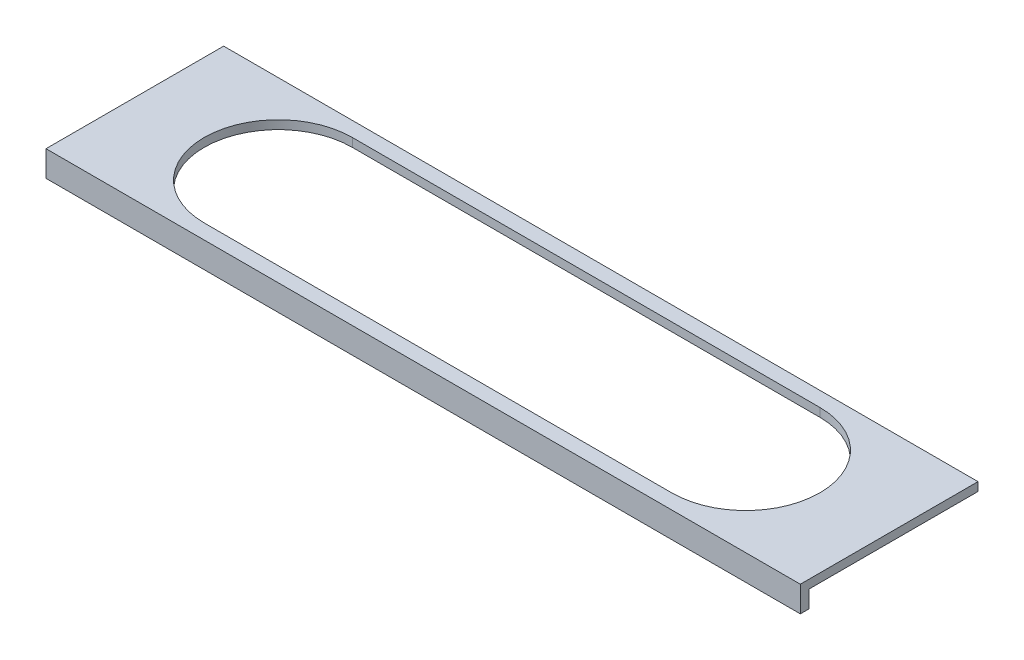
SolidWorks part; units mm, degrees
ref_plane "Front Plane" through (0, 0, 0) normal (0, 0, 1) x (1, 0, 0)
ref_plane "Top Plane" through (0, 0, 0) normal (0, 1, 0) x (1, 0, 0)
ref_plane "Right Plane" through (0, 0, 0) normal (1, 0, 0) x (0, 0, -1)
sketch "Sketch1" plane through (0, 0, 0) normal (0, 1, 0) x (1, 0, 0)
  line L1 (-4840, 1140) -> (4840, 1140)
  line L2 (-4840, 1140) -> (-4840, -1140)
  line L3 (-4840, -1140) -> (4840, -1140)
  line L4 (4840, 1140) -> (4840, -1140)
  line L5 (-4840, 1140) -> (4840, -1140) construction
  line L6 (-4840, -1140) -> (4840, 1140) construction
  point P0 (0, 0)
  dimension "D1" = 2280
  dimension "D2" = 9680
extrude "Boss-Extrude1" add sketch "Sketch1" along normal blind 110
sketch "Sketch2" plane through (0, 110, 0) normal (0, 1, 0) x (1, 0, 0)
  line L1 (-3000, 950) -> (3000, 950)
  line L3 (-3000, -950) -> (3000, -950)
  line L5 (-3000, 950) -> (3000, -950) construction
  line L6 (-3000, -950) -> (3000, 950) construction
  arc A0 (-3000, 950) -> (-3000, -950) centre (-3000, 0) ccw
  arc A1 (3000, -950) -> (3000, 950) centre (3000, 0) ccw
  point P0 (0, 0)
  dimension "D1" = 1900
  dimension "D2" = 6000
extrude "Cut-Extrude1" cut sketch "Sketch2" against normal blind 110
sketch "Sketch4" plane through (0, 0, 0) normal (0, -1, 0) x (1, 0, 0)
  line L0 (-4840, 1140) -> (-4840, 1030)
  line L1 (-4840, -1140) -> (-4840, 1140) construction
  line L2 (-4840, 1030) -> (4840, 1030)
  line L3 (4840, 1140) -> (4840, -1140) construction
  line L4 (4840, 1030) -> (4840, 1140)
  line L5 (4840, 1140) -> (-4840, 1140)
extrude "Boss-Extrude3" add sketch "Sketch4" along normal blind 220
